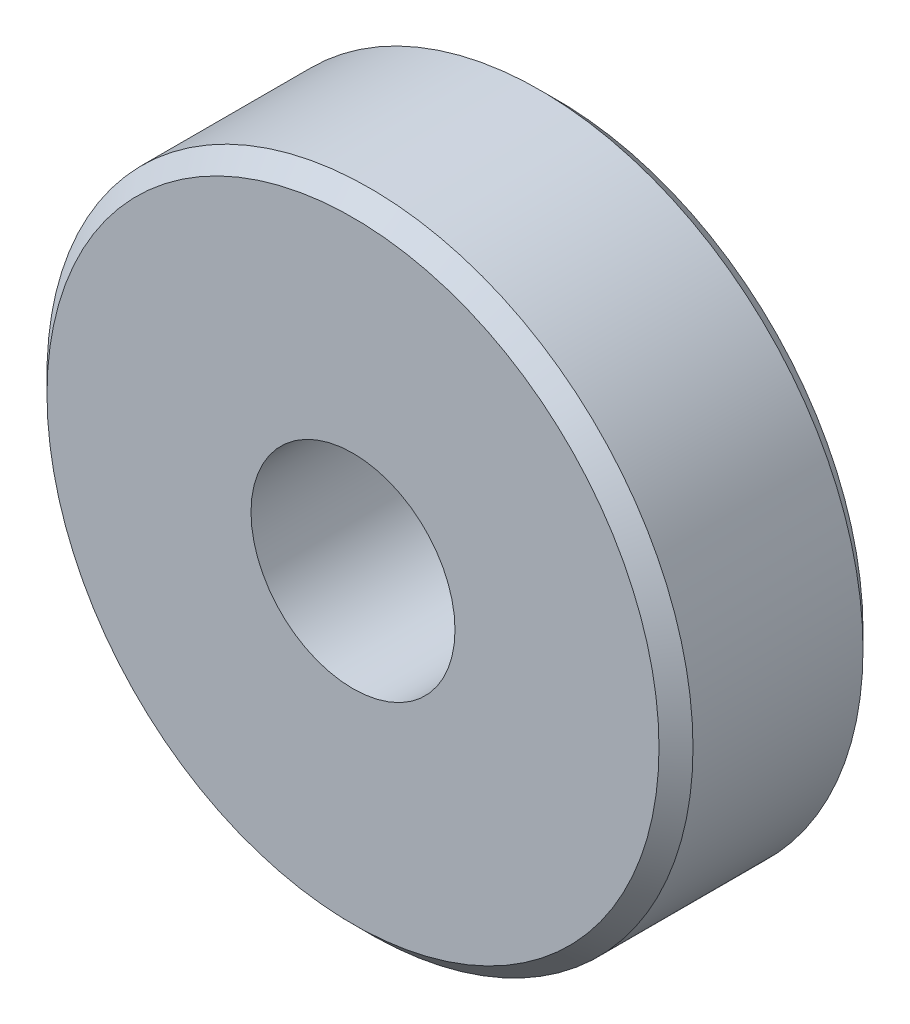
SolidWorks part; units mm, degrees
ref_plane "Front Plane" through (0, 0, 0) normal (0, 0, 1) x (1, 0, 0)
ref_plane "Top Plane" through (0, 0, 0) normal (0, 1, 0) x (1, 0, 0)
ref_plane "Right Plane" through (0, 0, 0) normal (1, 0, 0) x (0, 0, -1)
sketch "Sketch1" plane through (0, 0, 0) normal (0, 0, 1) x (1, 0, 0)
  circle A0 centre (0, 0) radius 9.5
  circle A1 centre (0, 0) radius 3
  dimension "D1" = 19
  dimension "D2" = 6
extrude "Boss-Extrude1" add sketch "Sketch1" along normal mid plane 6
chamfer "Chamfer1" distance 0.5 angle 45 2 edges at (9.5, 0, -3) (9.5, 0, 3)
